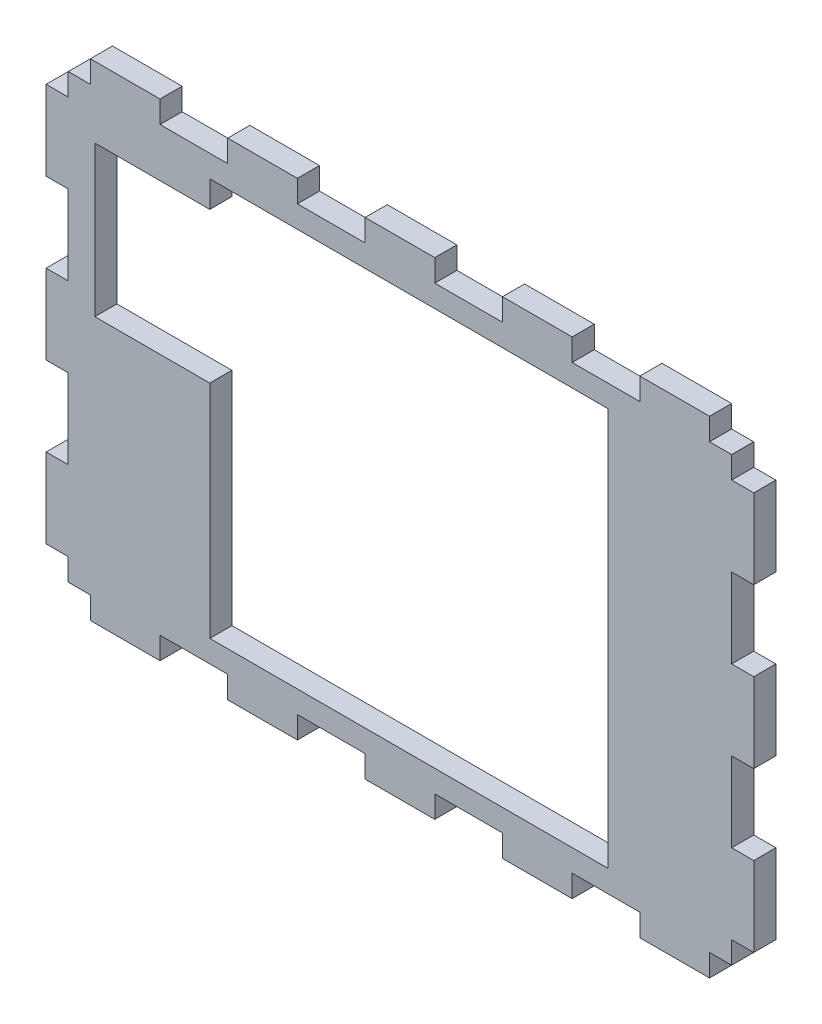
SolidWorks part; units mm, degrees
ref_plane "Front Plane" through (0, 0, 0) normal (0, 0, 1) x (1, 0, 0)
ref_plane "Top Plane" through (0, 0, 0) normal (0, 1, 0) x (1, 0, 0)
ref_plane "Right Plane" through (0, 0, 0) normal (1, 0, 0) x (0, 0, -1)
sketch "Sketch1" plane through (0, 0, 0) normal (0, 0, 1) x (1, 0, 0)
  line L1 (-75, 50) -> (-70, 50)
  line L2 (-75, 50) -> (-75, 45)
  line L3 (-75, -50) -> (-70, -50)
  line L4 (75, 50) -> (75, 45)
  line L5 (-75, 50) -> (75, -50) construction
  line L6 (-75, -50) -> (75, 50) construction
  line L7 (-75, 45) -> (-80, 45)
  line L9 (-75, 27) -> (-80, 27)
  line L10 (-80, 45) -> (-80, 27)
  line L11 (-75, 9) -> (-80, 9)
  line L12 (-80, 9) -> (-80, -9)
  line L13 (-75, -9) -> (-80, -9)
  line L15 (-75, -27) -> (-80, -27)
  line L16 (-80, -27) -> (-80, -45)
  line L17 (-75, -45) -> (-80, -45)
  line L18 (-80, -50) -> (-80, -45) construction
  line L19 (-80, 45) -> (-80, 50) construction
  line L20 (0, 55) -> (0, -55) construction
  line L21 (75, -27) -> (80, -27)
  line L22 (80, -27) -> (80, -45)
  line L23 (75, -45) -> (80, -45)
  line L25 (75, 9) -> (80, 9)
  line L26 (80, 9) -> (80, -9)
  line L27 (75, -9) -> (80, -9)
  line L29 (75, 27) -> (80, 27)
  line L30 (80, 45) -> (80, 27)
  line L31 (75, 45) -> (80, 45)
  line L33 (-38.9375, 50) -> (-38.9375, 55)
  line L35 (-70, 50) -> (-70, 55)
  line L36 (-70, 55) -> (-54.25, 55)
  line L37 (-54.25, 50) -> (-54.25, 55)
  line L39 (-23.1875, 50) -> (-23.1875, 55)
  line L40 (-38.9375, 55) -> (-23.1875, 55)
  line L41 (-7.875, 50) -> (-7.875, 55)
  line L43 (7.875, 50) -> (7.875, 55)
  line L44 (-7.875, 55) -> (7.875, 55)
  line L45 (23.1875, 50) -> (23.1875, 55)
  line L47 (38.9375, 50) -> (38.9375, 55)
  line L48 (23.1875, 55) -> (38.9375, 55)
  line L49 (54.25, 50) -> (54.25, 55)
  line L51 (70, 50) -> (70, 55)
  line L52 (54.25, 55) -> (70, 55)
  line L53 (-70, 55) -> (-75, 55) construction
  line L54 (70, 55) -> (75, 55) construction
  line L55 (-80, 0) -> (80, 0) construction
  line L57 (70, -50) -> (70, -55)
  line L58 (54.25, -55) -> (70, -55)
  line L59 (54.25, -50) -> (54.25, -55)
  line L61 (38.9375, -50) -> (38.9375, -55)
  line L62 (23.1875, -55) -> (38.9375, -55)
  line L63 (23.1875, -50) -> (23.1875, -55)
  line L65 (7.875, -50) -> (7.875, -55)
  line L66 (-7.875, -55) -> (7.875, -55)
  line L67 (-7.875, -50) -> (-7.875, -55)
  line L69 (-23.1875, -50) -> (-23.1875, -55)
  line L70 (-38.9375, -55) -> (-23.1875, -55)
  line L71 (-38.9375, -50) -> (-38.9375, -55)
  line L72 (-70, -55) -> (-54.25, -55)
  line L73 (-54.25, -50) -> (-54.25, -55)
  line L75 (-70, -50) -> (-70, -55)
  line L76 (-54.25, 50) -> (-38.9375, 50)
  line L77 (-23.1875, 50) -> (-7.875, 50)
  line L78 (7.875, 50) -> (23.1875, 50)
  line L79 (38.9375, 50) -> (54.25, 50)
  line L80 (70, 50) -> (75, 50)
  line L81 (75, 27) -> (75, 9)
  line L82 (75, -9) -> (75, -27)
  line L83 (75, -45) -> (75, -50)
  line L84 (70, -50) -> (75, -50)
  line L85 (38.9375, -50) -> (54.25, -50)
  line L86 (7.875, -50) -> (23.1875, -50)
  line L87 (-23.1875, -50) -> (-7.875, -50)
  line L88 (-54.25, -50) -> (-38.9375, -50)
  line L89 (-75, -45) -> (-75, -50)
  line L92 (-75, -9) -> (-75, -27)
  line L93 (-75, 27) -> (-75, 9)
  point P0 (0, 0)
  dimension "D1" = 150
  dimension "D2" = 100
  dimension "D3" = 5
  dimension "D4" = 5
  dimension "D5" = 18
  dimension "D7" = 15.75
  dimension "D8" = 5
  dimension "D9" = 5
  dimension "D6" = 3
  dimension "D10" = 5
extrude "Boss-Extrude1" add sketch "Sketch1" along normal blind 5
sketch "Sketch2" plane through (0, 0, 0) normal (0, 0, -1) x (-1, 0, 0)
  line L0 (-75, 9) -> (-75, 27) construction
  line L1 (-47, 45) -> (43, 45)
  line L2 (-47, 45) -> (-47, -45)
  line L3 (-47, -45) -> (43, -45)
  line L4 (43, 45) -> (43, 39)
  line L5 (43, 39) -> (69, 39)
  line L7 (43, 5) -> (69, 5)
  line L8 (69, 39) -> (69, 5)
  line L9 (38.9375, 50) -> (54.25, 50) construction
  line L10 (43, 5) -> (43, -45)
  point P11 (-47, 0)
  dimension "D1" = 90
  dimension "D2" = 90
  dimension "D3" = 28
  dimension "D4" = 34
  dimension "D5" = 26
  dimension "D6" = 11
extrude "Cut-Extrude1" cut sketch "Sketch2" against normal through all
